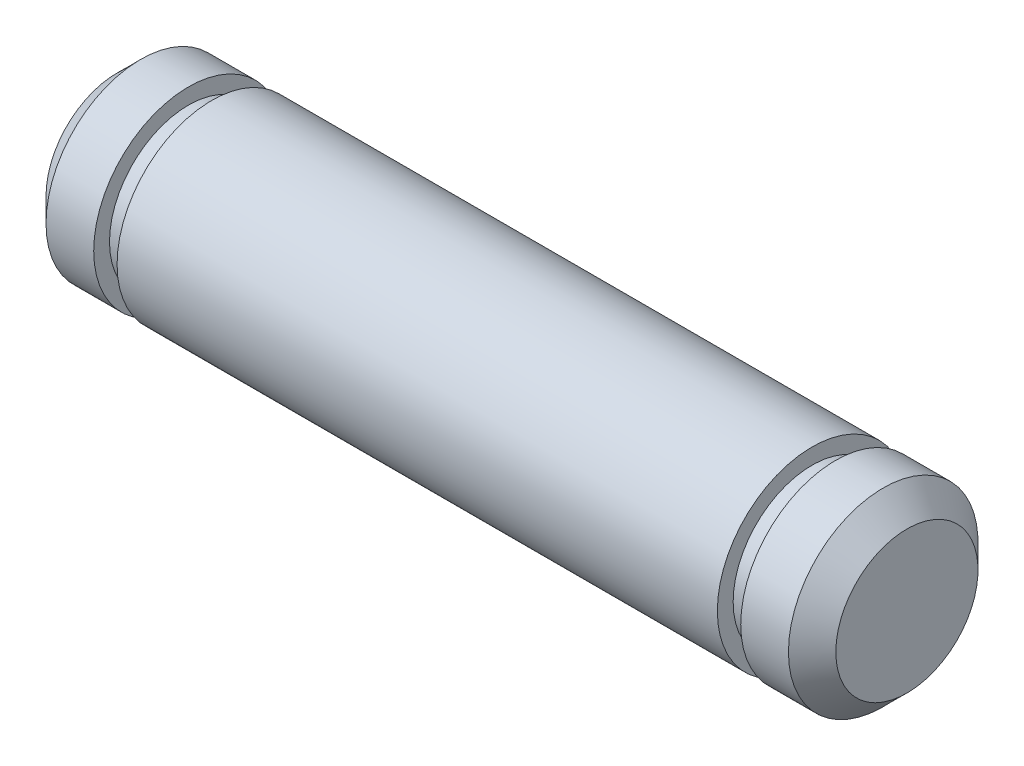
SolidWorks part; units mm, degrees
ref_plane "Front Plane" through (0, 0, 0) normal (0, 0, 1) x (1, 0, 0)
ref_plane "Top Plane" through (0, 0, 0) normal (0, 1, 0) x (1, 0, 0)
ref_plane "Right Plane" through (0, 0, 0) normal (1, 0, 0) x (0, 0, -1)
ref_plane "Plane1" through (0, 0, 0) normal (0, 0, 1) x (1, 0, 0)
sketch "Sketch1" plane through (0, 0, 0) normal (0, 0, 1) x (1, 0, 0)
  line L0 (-12.5, 0) -> (-12.5, 3)
  line L1 (-12.5, 3) -> (12.5, 3)
  line L2 (12.5, 3) -> (12.5, 0)
  line L3 (12.5, 0) -> (-12.5, 0)
  line L4 (12.5, 0) -> (-12.5, 0) construction
revolve "Revolve1" add sketch "Sketch1" angle 360 about L4
ref_plane "Plane2" through (0, 0, 0) normal (0, 0, 1) x (1, 0, 0)
sketch "Sketch2" plane through (0, 0, 0) normal (0, 0, 1) x (1, 0, 0)
  line L0 (11.75, 3) -> (12.5, 2.25)
  line L1 (12.5, 2.25) -> (12.5, 3)
  line L2 (12.5, 3) -> (11.75, 3)
  line L3 (12.5, 0) -> (-12.5, 0) construction
revolve "Cut-Revolve1" cut sketch "Sketch2" angle 360 about L3
ref_plane "Plane3" through (0, 0, 0) normal (0, 0, 1) x (1, 0, 0)
sketch "Sketch3" plane through (0, 0, 0) normal (0, 0, 1) x (1, 0, 0)
  line L0 (-12.5, 2.25) -> (-11.75, 3)
  line L1 (-11.75, 3) -> (-12.5, 3)
  line L2 (-12.5, 3) -> (-12.5, 2.25)
  line L3 (12.5, 0) -> (-12.5, 0) construction
revolve "Cut-Revolve2" cut sketch "Sketch3" angle 360 about L3
ref_plane "Plane4" through (0, 0, 0) normal (0, 0, 1) x (1, 0, 0)
sketch "Sketch4" plane through (0, 0, 0) normal (0, 0, 1) x (1, 0, 0)
  line L0 (9.5, 2.5) -> (10.24, 2.5)
  line L1 (10.24, 2.5) -> (10.24, 3)
  line L2 (10.24, 3) -> (9.5, 3)
  line L3 (9.5, 3) -> (9.5, 2.5)
  line L4 (12.5, 0) -> (-12.5, 0) construction
revolve "Cut-Revolve3" cut sketch "Sketch4" angle 360 about L4
ref_plane "Plane5" through (0, 0, 0) normal (0, 0, 1) x (1, 0, 0)
sketch "Sketch5" plane through (0, 0, 0) normal (0, 0, 1) x (1, 0, 0)
  line L0 (-10.24, 2.5) -> (-9.5, 2.5)
  line L1 (-9.5, 2.5) -> (-9.5, 3)
  line L2 (-9.5, 3) -> (-10.24, 3)
  line L3 (-10.24, 3) -> (-10.24, 2.5)
  line L4 (12.5, 0) -> (-12.5, 0) construction
revolve "Cut-Revolve4" cut sketch "Sketch5" angle 360 about L4
